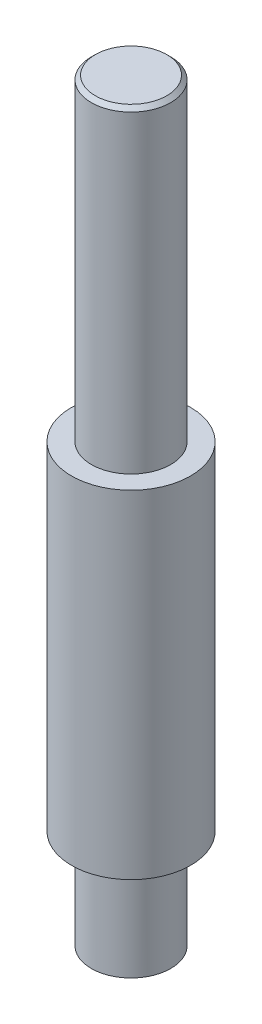
SolidWorks part; units mm, degrees
material "Plain Carbon Steel"
ref_plane "Front Plane" through (0, 0, 0) normal (0, 0, 1) x (1, 0, 0)
ref_plane "Top Plane" through (0, 0, 0) normal (0, 1, 0) x (1, 0, 0)
ref_plane "Right Plane" through (0, 0, 0) normal (1, 0, 0) x (0, 0, -1)
sketch "Sketch1" plane through (0, 0, 0) normal (0, 1, 0) x (1, 0, 0)
  circle A0 centre (0, 0) radius 10
  dimension "D1" = 20
extrude "Boss-Extrude1" add sketch "Sketch1" along normal mid plane 190
ref_plane "Plane2" through (0, -70, 0) normal (0, -1, 0) x (-1, 0, 0)
sketch "Sketch3" plane through (0, -70, 0) normal (0, -1, 0) x (-1, 0, 0)
  circle A0 centre (0, 0) radius 14.99
  dimension "D1" = 29.98
extrude "Boss-Extrude2" add sketch "Sketch3" against normal blind 85
chamfer "Chamfer1" distance 1 angle 45 1 edges at (0, 95, 10)
